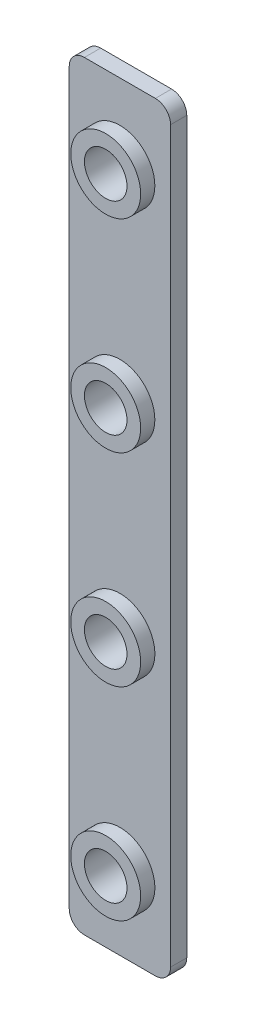
SolidWorks part; units mm, degrees
material "Plain Carbon Steel"
ref_plane "Front Plane" through (0, 0, 0) normal (0, 0, 1) x (1, 0, 0)
ref_plane "Top Plane" through (0, 0, 0) normal (0, 1, 0) x (1, 0, 0)
ref_plane "Right Plane" through (0, 0, 0) normal (1, 0, 0) x (0, 0, -1)
sketch "Sketch1" plane through (0, 0, 0) normal (0, 0, 1) x (1, 0, 0)
  line L1 (3.5, -37.5) -> (-3.5, -37.5)
  line L2 (5, -36) -> (5, 36)
  line L3 (3.5, 37.5) -> (-3.5, 37.5)
  line L4 (-5, -36) -> (-5, 36)
  line L5 (5, -37.5) -> (-5, 37.5) construction
  line L6 (5, 37.5) -> (-5, -37.5) construction
  arc A0 (3.5, -37.5) -> (5, -36) centre (3.5, -36) ccw
  arc A1 (-3.5, -37.5) -> (-5, -36) centre (-3.5, -36) cw
  arc A2 (-3.5, 37.5) -> (-5, 36) centre (-3.5, 36) ccw
  arc A3 (5, 36) -> (3.5, 37.5) centre (3.5, 36) ccw
  point P0 (0, 0)
  dimension "D3" = 1.5
  dimension "D1" = 75
  dimension "D2" = 10
extrude "Boss-Extrude1" add sketch "Sketch1" along normal blind 1.6
sketch "Sketch2" plane through (0, 0, 1.6) normal (0, 0, 1) x (1, 0, 0)
  line L0 (-10, 0) -> (0, 0) construction
  line L2 (0, 0) -> (0, 41.985) construction
  circle A0 centre (0, 10) radius 3.45
  circle A1 centre (0, 30) radius 3.45
  circle A2 centre (0, -10) radius 3.45
  circle A3 centre (0, -30) radius 3.45
  dimension "D1" = 6.9
  dimension "D3" = 10
  dimension "D2" = 20
extrude "Boss-Extrude2" add sketch "Sketch2" along normal blind 1.4
hole_wizard "M5x0.8 Tapped Hole1" positions "Sketch4" profile "Sketch3" tap size "M5x0.8" standard "ANSI Metric" end condition through all
sketch "Sketch4" plane through (0, 0, 3) normal (0, 0, 1) x (1, 0, 0)
  point P0 (0, 30)
  point P3 (0, 10)
  point P6 (0, -10)
  point P9 (0, -30)
sketch "Sketch3" plane through (0, 30, 3) normal (1, 0, 0) x (0, -1, 0)
  line L0 (0, 0) -> (0, 3)
  line L1 (0, 3) -> (2.1, 3)
  line L2 (2.1, 3) -> (2.1, 0)
  line L5 (2.1, 0) -> (0, 0)
  line L11 (0, -6.35) -> (0, 107.95) construction
  dimension "Thru Tap Drill Dia." = 4.2
  dimension "Thru Tap Drill Depth" = 3
cosmetic thread "Hole Thread1" parameters "D2"=5
cosmetic thread "Hole Thread2" parameters "D2"=5
cosmetic thread "Hole Thread3" parameters "D2"=5
cosmetic thread "Hole Thread4" parameters "D2"=5
